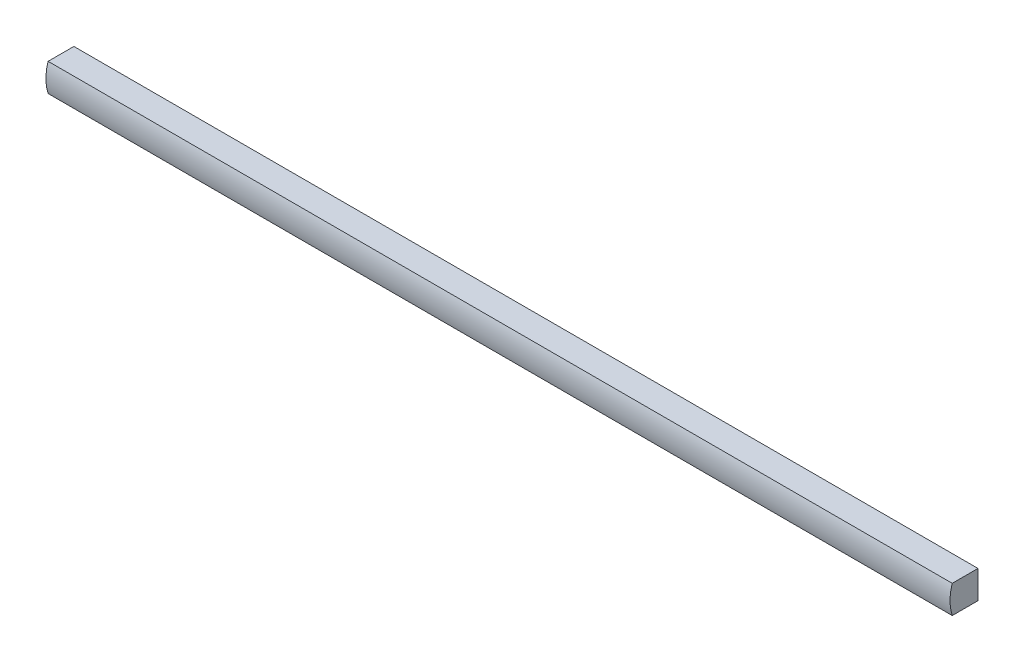
SolidWorks part; units mm, degrees
material "Plywood"
ref_plane "Front Plane" through (0, 0, 0) normal (0, 0, 1) x (1, 0, 0)
ref_plane "Top Plane" through (0, 0, 0) normal (0, 1, 0) x (1, 0, 0)
ref_plane "Right Plane" through (0, 0, 0) normal (1, 0, 0) x (0, 0, -1)
sketch "Sketch1" plane through (0, 0, 0) normal (1, 0, 0) x (0, 0, -1)
  line L1 (0, 0) -> (9.525, 0)
  line L2 (0, 0) -> (0, 9.525)
  line L3 (0, 9.525) -> (9.525, 9.525)
  line L4 (9.525, 0) -> (9.525, 9.525)
  arc A0 (0.7556, 0) -> (0.7426, 9.525) centre (15.5137, 4.7827) cw
  dimension "D2" = 8.7824
  dimension "D1" = 9.525
  dimension "D3" = 8.7694
extrude "Boss-Extrude1" add sketch "Sketch1" against normal blind 307.975 contours L1 L4 L3 L2
move or copy body "Body-Move/Copy1" [suppressed] bodies to move or copy 101 parameters "D1"=0, "D2"=0, "D3"=0
